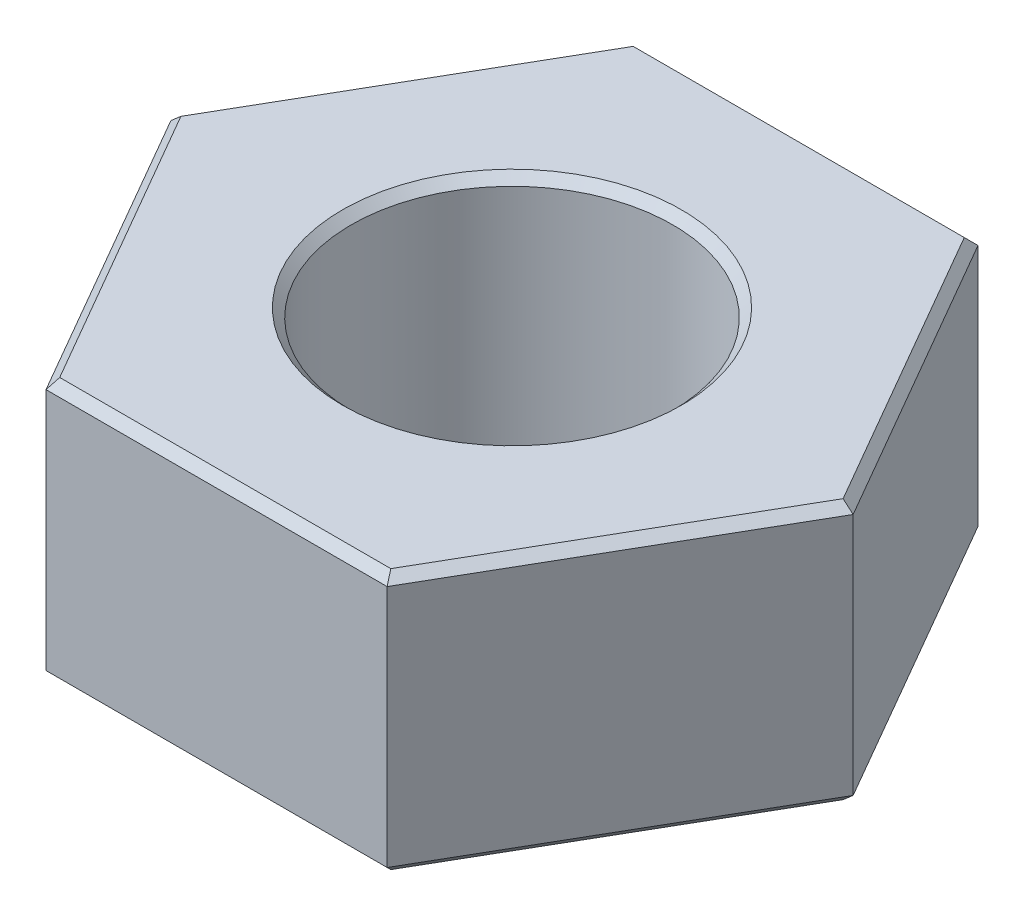
SolidWorks part; units mm, degrees
material "1023 Листовая углеродистая сталь (SS)"
ref_plane "Спереди" through (0, 0, 0) normal (0, 0, 1) x (1, 0, 0)
ref_plane "Сверху" through (0, 0, 0) normal (0, 1, 0) x (1, 0, 0)
ref_plane "Справа" through (0, 0, 0) normal (1, 0, 0) x (0, 0, -1)
sketch "Эскиз1" plane through (0, 0, 0) normal (0, 1, 0) x (1, 0, 0)
  line L1 (3.926, 0) -> (1.963, 3.4)
  line L2 (1.963, 3.4) -> (-1.963, 3.4)
  line L3 (-1.963, 3.4) -> (-3.926, 0)
  line L4 (-3.926, 0) -> (-1.963, -3.4)
  line L5 (-1.963, -3.4) -> (1.963, -3.4)
  line L6 (1.963, -3.4) -> (3.926, 0)
  circle A0 centre (0, 0) radius 3.4 construction
  circle A1 centre (0, 0) radius 1.85
  dimension "D1" = 6.8
  dimension "D2" = 3.7
extrude "Бобышка-Вытянуть1" add sketch "Эскиз1" along normal blind 3
chamfer "Фаска1" distance 0.1 angle 45 14 edges at (0, 0, -3.4) (-2.9445, 0, -1.7) (-2.9445, 0, 1.7) (0, 0, 3.4) (2.9445, 0, 1.7) (2.9445, 0, -1.7) (0, 0, 1.85) (0, 3, -3.4) (-2.9445, 3, -1.7) (2.9445, 3, -1.7) (2.9445, 3, 1.7) (-2.9445, 3, 1.7) (0, 3, 3.4) (0, 3, 1.85)
